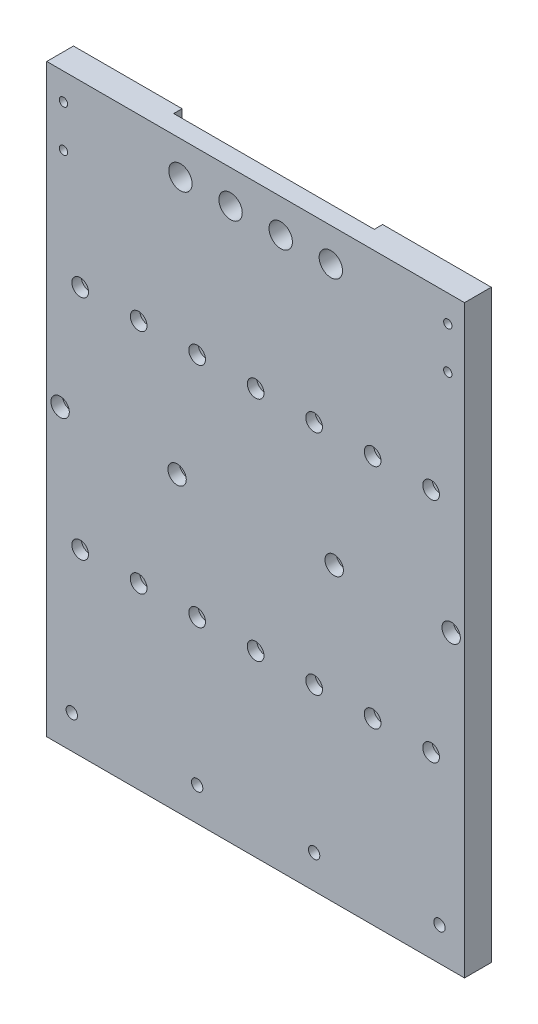
SolidWorks part; units mm, degrees
ref_plane "前视基准面" through (0, 0, 0) normal (0, 0, 1) x (1, 0, 0)
ref_plane "上视基准面" through (0, 0, 0) normal (0, 1, 0) x (1, 0, 0)
ref_plane "右视基准面" through (0, 0, 0) normal (1, 0, 0) x (0, 0, -1)
sketch "草图1" plane through (0, 0, 0) normal (0, 0, 1) x (1, 0, 0)
  line L1 (-125, 175) -> (125, 175)
  line L2 (-125, 175) -> (-125, -175)
  line L3 (-125, -175) -> (125, -175)
  line L4 (125, 175) -> (125, -175)
  line L5 (-125, 175) -> (125, -175) construction
  line L6 (-125, -175) -> (125, 175) construction
  point P0 (0, 0)
  dimension "D1" = 250
  dimension "D2" = 350
extrude "凸台-拉伸1" add sketch "草图1" along normal blind 16
sketch "草图2" plane through (0, 0, 16) normal (0, 0, 1) x (1, 0, 0)
  line L0 (-105, 68) -> (105, 68)
  line L3 (-125, 175) -> (-125, -175) construction
  line L4 (125, -175) -> (125, 175) construction
  line L6 (-127.8594, 0) -> (125, 0) construction
  line L8 (-105, -68) -> (105, -68)
  point P10 (-70, 68)
  point P11 (-35, 68)
  point P12 (0, 68)
  point P13 (35, 68)
  point P14 (70, 68)
  point P23 (70, -68)
  point P24 (35, -68)
  point P26 (0, -68)
  point P28 (-35, -68)
  point P29 (-70, -68)
  dimension "D1" = 20
  dimension "D2" = 20
  dimension "D3" = 68
hole_wizard "打孔尺寸(%根据)内六角圆柱头螺钉的类型0" positions "3D草图1" profile "草图3" counterbore size "M5" standard "GB"
sketch3d "3D草图1"
  point P6 (-70, 68, 16)
  point P9 (-35, 68, 16)
  point P12 (0, 68, 16)
  point P15 (35, 68, 16)
  point P18 (70, 68, 16)
  point P46 (-105, 68, 16)
  point P49 (105, 68, 16)
  point P63 (-105, -68, 16)
  point P66 (-70, -68, 16)
  point P69 (-35, -68, 16)
  point P72 (0, -68, 16)
  point P75 (35, -68, 16)
  point P78 (70, -68, 16)
  point P81 (105, -68, 16)
sketch "草图3" plane through (-70, 68, 16) normal (1, 0, 0) x (0, -1, 0)
  line L0 (0, 0) -> (0, 23.9024)
  line L1 (0, 23.9024) -> (2.75, 22.25)
  line L2 (2.75, 22.25) -> (2.75, 5.7)
  line L3 (2.75, 5.7) -> (5, 5.7)
  line L4 (5, 5.7) -> (5, 0)
  line L5 (5, 0) -> (0, 0)
  line L10 (0, 23.9024) -> (-2.75, 22.25) construction
  line L11 (0, -6.35) -> (0, 107.95) construction
  dimension "孔直径" = 5.5
  dimension "孔深度" = 22.25
  dimension "柱形沉头孔直径" = 10
  dimension "柱形沉头孔深度" = 5.7
  dimension "导头角度" = 118
sketch "草图4" plane through (0, 0, 16) normal (0, 0, 1) x (1, 0, 0)
  line L0 (-117, 0) -> (117, 0) construction
  line L1 (0, 3.9926) -> (0, 30.4117) construction
  line L3 (125, -175) -> (125, 175) construction
  line L6 (-125, 175) -> (-125, -175) construction
  point P8 (-47, 0)
  point P9 (47, 0)
  dimension "D1" = 94
  dimension "D2" = 70
  dimension "D3" = 0
  dimension "D4" = 70
  dimension "D5" = 8
  dimension "D6" = 8
hole_wizard "打孔尺寸(%根据)内六角圆柱头螺钉的类型0" positions "3D草图2" profile "草图5" counterbore size "M6" standard "GB" end condition up to next
sketch3d "3D草图2"
  point P6 (-47, 0, 16)
  point P9 (47, 0, 16)
  point P14 (-117, 0, 16)
  point P17 (117, 0, 16)
sketch "草图5" plane through (-47, 0, 16) normal (1, 0, 0) x (0, -1, 0)
  line L0 (0, 0) -> (0, 16)
  line L1 (0, 16) -> (3.3, 16)
  line L3 (3.3, 16) -> (3.3, 6.8)
  line L4 (3.3, 6.8) -> (5.5, 6.8)
  line L5 (5.5, 6.8) -> (5.5, 0)
  line L7 (5.5, 0) -> (0, 0)
  line L11 (0, -6.35) -> (0, 107.95) construction
  dimension "通孔孔直径" = 6.6
  dimension "通孔孔深度" = 16
  dimension "柱形沉头孔直径" = 11
  dimension "柱形沉头孔深度" = 6.8
sketch "草图6" plane through (0, 0, 16) normal (0, 0, 1) x (1, 0, 0)
  line L0 (-110, -155) -> (-35, -155)
  line L1 (-125, -175) -> (125, -175) construction
  line L2 (-125, 175) -> (-125, -175) construction
  line L3 (0, -175) -> (0, -91.9887) construction
  line L4 (110, -155) -> (35, -155)
  dimension "D1" = 20
  dimension "D2" = 15
  dimension "D3" = 75
  dimension "D4" = 70
hole_wizard "大小mm 暗销孔1" positions "3D草图3" profile "草图7" hole size "Ø8.0" standard "GB"
sketch3d "3D草图3"
  point P0 (-110, -155, 16)
  point P3 (-35, -155, 16)
  point P6 (35, -155, 16)
  point P9 (110, -155, 16)
sketch "草图7" plane through (-110, -155, 16) normal (1, 0, 0) x (0, -1, 0)
  line L0 (0, 0) -> (0, 24.2929)
  line L1 (0, 24.2929) -> (3.4, 22.25)
  line L2 (3.4, 22.25) -> (3.4, 0)
  line L5 (3.4, 0) -> (0, 0)
  line L10 (0, 24.2929) -> (-3.4, 22.25) construction
  line L11 (0, -6.35) -> (0, 107.95) construction
  dimension "孔直径" = 6.8
  dimension "孔深度" = 22.25
  dimension "导头角度" = 118
sketch "草图8" plane through (0, 0, 16) normal (0, 0, 1) x (1, 0, 0)
  line L0 (-115, 159) -> (-115, 134) construction
  line L1 (125, 175) -> (-125, 175) construction
  line L2 (0, 175) -> (0, 124.2998) construction
  line L3 (-125, 175) -> (-125, -175) construction
  line L4 (115, 159) -> (115, 134) construction
  dimension "D1" = 25
  dimension "D2" = 10
  dimension "D3" = 16
hole_wizard "M6 螺纹孔1" positions "3D草图4" profile "草图9" tap size "M6" standard "GB"
sketch3d "3D草图4"
  point P0 (-115, 159, 16)
  point P3 (-115, 134, 16)
  point P6 (115, 159, 16)
  point P9 (115, 134, 16)
sketch "草图9" plane through (-115, 159, 16) normal (1, 0, 0) x (0, -1, 0)
  line L0 (0, 0) -> (0, 21.5022)
  line L1 (0, 21.5022) -> (2.5, 20)
  line L2 (2.5, 20) -> (2.5, 0)
  line L5 (2.5, 0) -> (0, 0)
  line L10 (0, 21.5022) -> (-2.5, 20) construction
  line L11 (0, -6.35) -> (0, 107.95) construction
  dimension "螺纹孔钻头直径" = 5
  dimension "螺纹孔钻头深度" = 20
  dimension "导头角度" = 118
cosmetic thread "孔螺蚊线1" parameters "D1"=12, "D2"=6
cosmetic thread "孔螺蚊线2" parameters "D1"=12, "D2"=6
cosmetic thread "孔螺蚊线3" parameters "D1"=12, "D2"=6
cosmetic thread "孔螺蚊线4" parameters "D1"=12, "D2"=6
sketch "草图10" plane through (0, 0, 16) normal (0, 0, 1) x (1, 0, 0)
  line L0 (-45, 155) -> (45, 155)
  line L1 (125, 175) -> (-125, 175) construction
  line L2 (-125, 175) -> (-125, -175) construction
  line L3 (0, 175) -> (0, 109.9484) construction
  point P5 (-15, 155)
  point P6 (15, 155)
  dimension "D1" = 20
  dimension "D2" = 90
  dimension "D3" = 30
  dimension "D4" = 80
hole_wizard "大小mm 暗销槽口2" positions "3D草图5" profile "草图11" size "Ø16.0" standard "GB" slot yes
sketch3d "3D草图5"
  point P0 (-45, 155, 16)
  point P3 (-15, 155, 16)
  point P6 (15, 155, 16)
  point P9 (45, 155, 16)
sketch "草图11" plane through (-45, 155, 16) normal (1, 0, 0) x (0, -1, 0)
  line L0 (0, 0) -> (0, 19.206)
  line L1 (0, 19.206) -> (7, 15)
  line L2 (7, 15) -> (7, 0)
  line L5 (7, 0) -> (0, 0)
  line L10 (0, 19.206) -> (-7, 15) construction
  line L11 (0, -6.35) -> (0, 107.95) construction
  dimension "孔直径" = 14
  dimension "孔深度" = 15
  dimension "导头角度" = 118
sketch "草图12" plane through (0, 0, 0) normal (0, 0, -1) x (-1, 0, 0)
  line L0 (-125, 175) -> (125, 175) construction
  line L1 (-60, 146) -> (60, 146)
  line L2 (-60, 146) -> (-60, 175)
  line L3 (-60, 175) -> (60, 175)
  line L4 (60, 146) -> (60, 175)
  point P6 (0, 175)
  point P7 (0, 175)
  dimension "D1" = 29
  dimension "D2" = 0
  dimension "D3" = 120
extrude "切除-拉伸1" cut sketch "草图12" against normal blind 5
fillet "圆角1" radius 3 2 edges at (60, 146, 2.5) (-60, 146, 2.5)
